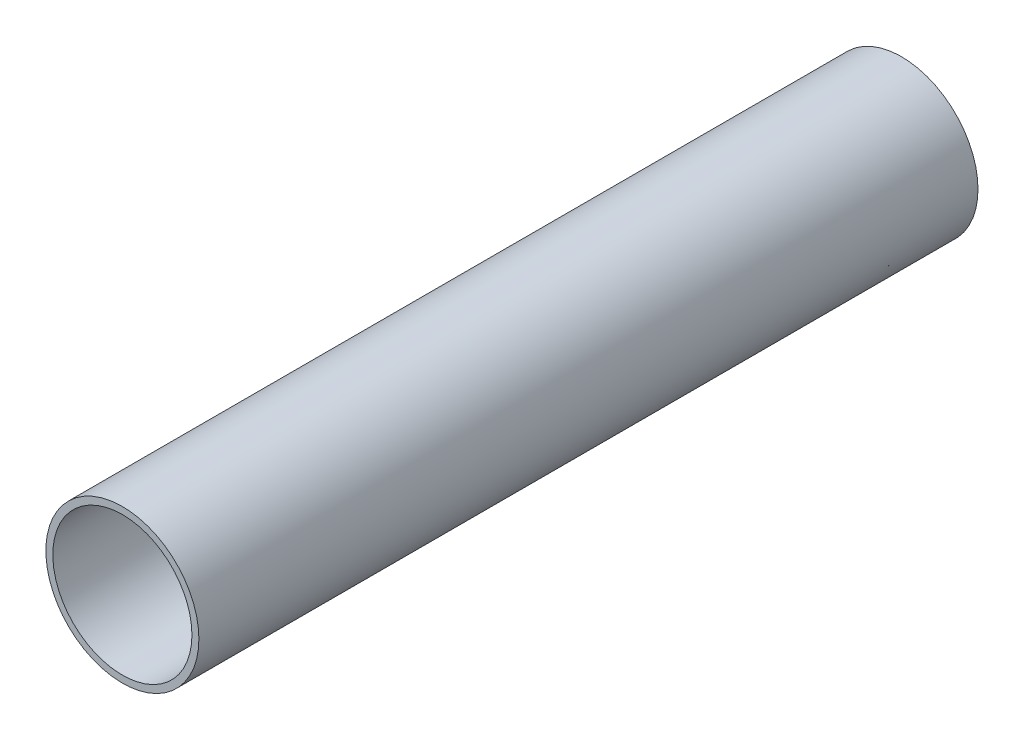
SolidWorks part; units mm, degrees
material "Laiton"
ref_plane "Plan de face" through (0, 0, 0) normal (0, 0, 1) x (1, 0, 0)
ref_plane "Plan de dessus" through (0, 0, 0) normal (0, 1, 0) x (1, 0, 0)
ref_plane "Plan de droite" through (0, 0, 0) normal (1, 0, 0) x (0, 0, -1)
sketch "Esquisse1" plane through (0, 0, 0) normal (0, 0, 1) x (1, 0, 0)
  circle A0 centre (0, 0) radius 5
  circle A1 centre (0, 0) radius 5.5
  dimension "D2" = 11
  dimension "D3" = 0.5
extrude "Boss.-Extru.1" add sketch "Esquisse1" along normal mid plane 56
sketch "Esquisse2" plane through (0, 0, 0) normal (0, 1, 0) x (1, 0, 0)
  line L0 (-5.5, -28) -> (5.5, -28) construction
  line L1 (5, 28) -> (-5, 28) construction
  circle A0 centre (0, -19.5) radius 1
  circle A1 centre (0, 27) radius 1
  dimension "D1" = 2
  dimension "D3" = 1
  dimension "D2" = 8.5
extrude "Boss.-Extru.2" add sketch "Esquisse2" along normal up to next and the other way up to next
